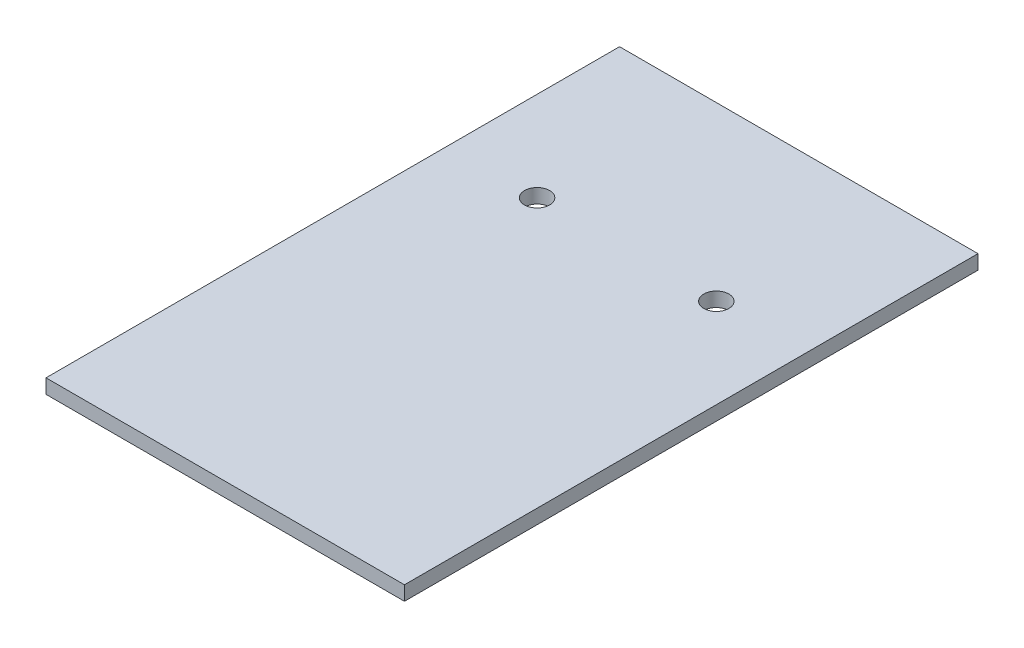
SolidWorks part; units mm, degrees
ref_plane "Plan de face" through (0, 0, 0) normal (0, 0, 1) x (1, 0, 0)
ref_plane "Plan de dessus" through (0, 0, 0) normal (0, 1, 0) x (1, 0, 0)
ref_plane "Plan de droite" through (0, 0, 0) normal (1, 0, 0) x (0, 0, -1)
sketch "Esquisse1" plane through (0, 0, 0) normal (0, 1, 0) x (1, 0, 0)
  line L1 (0, 0) -> (50, 0)
  line L2 (0, 0) -> (0, 80)
  line L3 (0, 80) -> (50, 80)
  line L4 (50, 0) -> (50, 80)
  dimension "D1" = 80
  dimension "D2" = 50
extrude "Boss.-Extru.1" add sketch "Esquisse1" along normal blind 2
sketch "Esquisse2" plane through (0, 2, 0) normal (0, 1, 0) x (1, 0, 0)
  line L0 (25, 80) -> (25, 24.8051) construction
  line L1 (50, 80) -> (0, 80) construction
  circle A0 centre (12.5, 56) radius 1.75
  circle A1 centre (37.5, 56) radius 1.75
  dimension "D1" = 3.5
  dimension "D2" = 12.5
  dimension "D3" = 24
extrude "Enlèv. mat.-Extru.1" cut sketch "Esquisse2" against normal up to next
